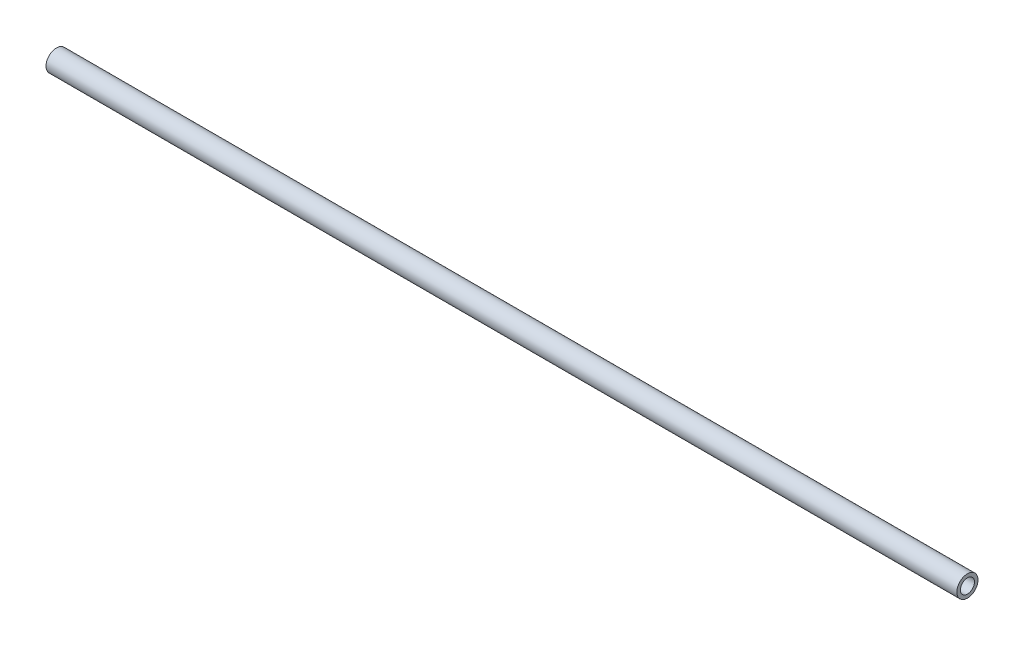
SolidWorks part; units mm, degrees
material "PVC 0.007 Plasticized"
ref_plane "Front" through (0, 0, 0) normal (0, 0, 1) x (1, 0, 0)
ref_plane "Top" through (0, 0, 0) normal (0, 1, 0) x (1, 0, 0)
ref_plane "Right" through (0, 0, 0) normal (1, 0, 0) x (0, 0, -1)
sketch "Sketch1" plane through (0, 0, 0) normal (1, 0, 0) x (0, 0, -1)
  circle A0 centre (0, 0) radius 4.7625
  circle A1 centre (0, 0) radius 3.175
  point P4 (4.7625, 0)
  point P5 (3.175, 0)
  dimension "OD" = 9.525
  dimension "ID" = 6.35
  dimension "Wall" = 1.5875
extrude "Extrude1" add sketch "Sketch1" along normal mid plane 410.464
